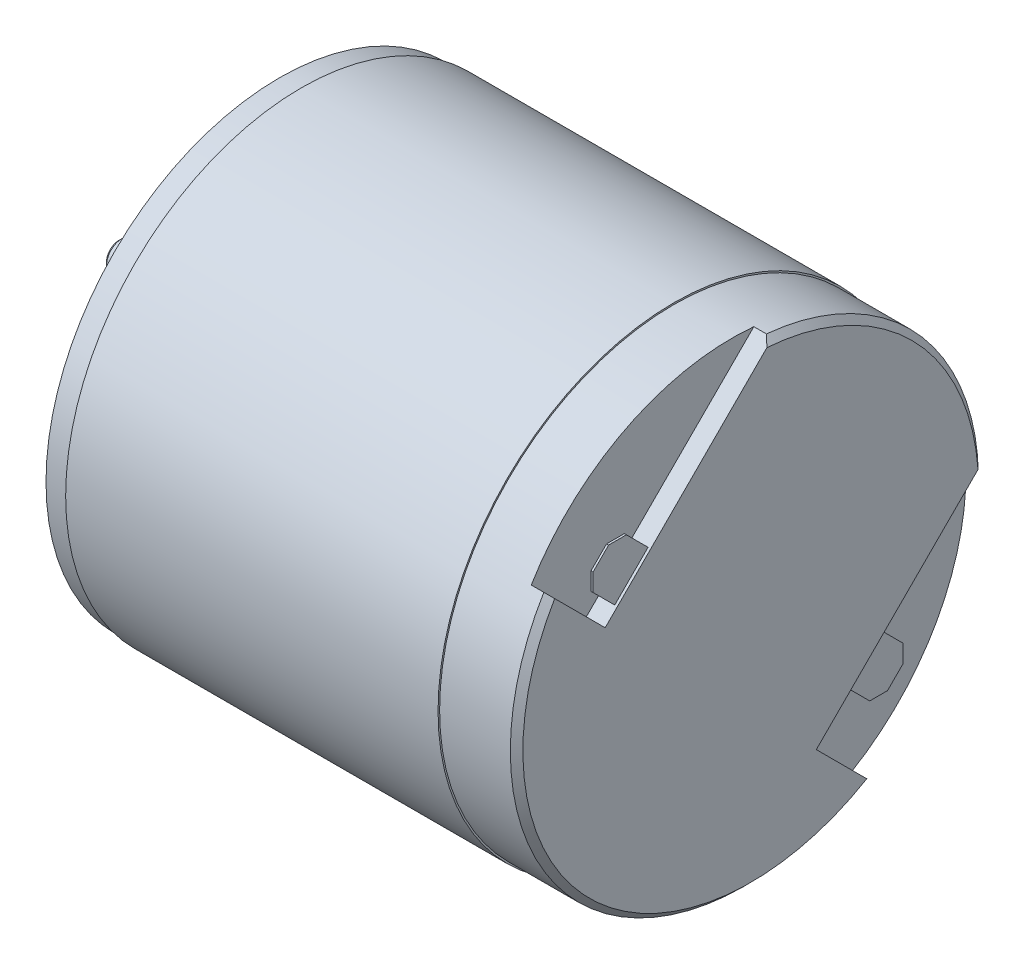
SolidWorks part; units mm, degrees
ref_plane "Plan de face" through (0, 0, 0) normal (0, 0, 1) x (1, 0, 0)
ref_plane "Plan de dessus" through (0, 0, 0) normal (0, 1, 0) x (1, 0, 0)
ref_plane "Plan de droite" through (0, 0, 0) normal (1, 0, 0) x (0, 0, -1)
sketch "Esquisse1" plane through (0, 0, 0) normal (0, 0, 1) x (1, 0, 0)
  line L0 (0, 0) -> (50.4998, 0) construction
  line L1 (0, 0) -> (0, 14.9)
  line L2 (0, 14.9) -> (-4.9, 14.9)
  line L3 (-4.9, 14.9) -> (-4.9, 15)
  line L4 (-4.9, 15) -> (-28.6, 15)
  line L5 (-28.6, 15) -> (-28.6, 14.85)
  line L6 (-28.6, 14.85) -> (-30, 14.85)
  line L7 (-30, 14.85) -> (-30, 4)
  line L8 (-30, 4) -> (-30.9, 4)
  line L9 (-30.9, 4) -> (-30.9, 2.1)
  line L10 (-40.2, 0) -> (0, 0)
  line L11 (-30.9, 2.1) -> (-32, 2.1)
  line L12 (-32, 2.1) -> (-32, 1)
  line L13 (-32, 1) -> (-40.2, 1)
  line L14 (-40.2, 1) -> (-40.2, 0)
  dimension "D1" = 30
  dimension "D2" = 29.8
  dimension "D3" = 29.7
  dimension "D4" = 30
  dimension "D5" = 4.9
  dimension "D6" = 1.4
  dimension "D7" = 8
  dimension "D8" = 2
  dimension "D9" = 8.2
  dimension "D10" = 4.2
  dimension "D11" = 2
  dimension "D12" = 1.1
revolve "Révolution1" add sketch "Esquisse1" angle 360 about L0
sketch "Esquisse2" plane through (0, 0, 0) normal (1, 0, 0) x (0, 0, -1)
  line L0 (0, 0) -> (0, 20.4929) construction
  line L1 (1.3991, 14.8342) -> (-9.2631, 4.1719)
  line L2 (-9.2631, 4.1719) -> (-12.7693, 7.6782)
  line L3 (14.8342, 1.3991) -> (4.1719, -9.2631)
  line L4 (4.1719, -9.2631) -> (7.6782, -12.7693)
  line L5 (0, 0) -> (16.0496, 16.0496) construction
  circle A0 centre (0, 0) radius 14.9 construction
  circle M1 centre (0, 0) radius 14.9
  dimension "D1" = 45
  dimension "D2" = 19
  dimension "D3" = 3.6
extrude "Enlèv. mat.-Extru.2" cut sketch "Esquisse2" against normal blind 1.2 contours L2 L1 M1 | L3 L4 M1
chamfer "Chanfrein1" distance 0.2 angle 45 1 edges at (-40.2, 0, 1)
ref_plane "Plan1" through (-0.3, 0, 0) normal (1, 0, 0) x (0, 0, -1)
sketch "Esquisse3" plane through (-0.3, 0, 0) normal (1, 0, 0) x (0, 0, -1)
  line L0 (-6.364, 7.0711) -> (-8.3085, 9.0156)
  line L1 (-8.3085, 9.0156) -> (-10.4298, 6.8943)
  line L2 (-10.4298, 6.8943) -> (-8.4853, 4.9497)
  line L3 (-8.4853, 4.9497) -> (-6.364, 7.0711)
  line L4 (8.4853, -4.9497) -> (6.364, -7.0711)
  line L5 (6.364, -7.0711) -> (8.3085, -9.0156)
  line L6 (8.3085, -9.0156) -> (10.4298, -6.8943)
  line L7 (10.4298, -6.8943) -> (8.4853, -4.9497)
  line L8 (1.3991, 14.8342) -> (-9.2631, 4.1719) construction
  line L9 (14.8342, 1.3991) -> (4.1719, -9.2631) construction
  dimension "D1" = 3
  dimension "D2" = 2.75
  dimension "D3" = 0.5
  dimension "D4" = 0.5
extrude "Extrusion1" add sketch "Esquisse3" along normal blind 0.13
chamfer "Chanfrein2" distance 0.8 angle 45 4 edges at (-0.235, -9.0156, -8.3085) (-0.235, -6.8943, -10.4298) (-0.235, 6.8943, 10.4298) (-0.235, 9.0156, 8.3085)
chamfer "Chanfrein3" distance 0.4 angle 45 2 edges at (0, -10.5359, 10.5359) (0, 10.5359, -10.5359)
chamfer "Chanfrein4" distance 0.2 angle 30 1 edges at (-32, 0, 2.1)
